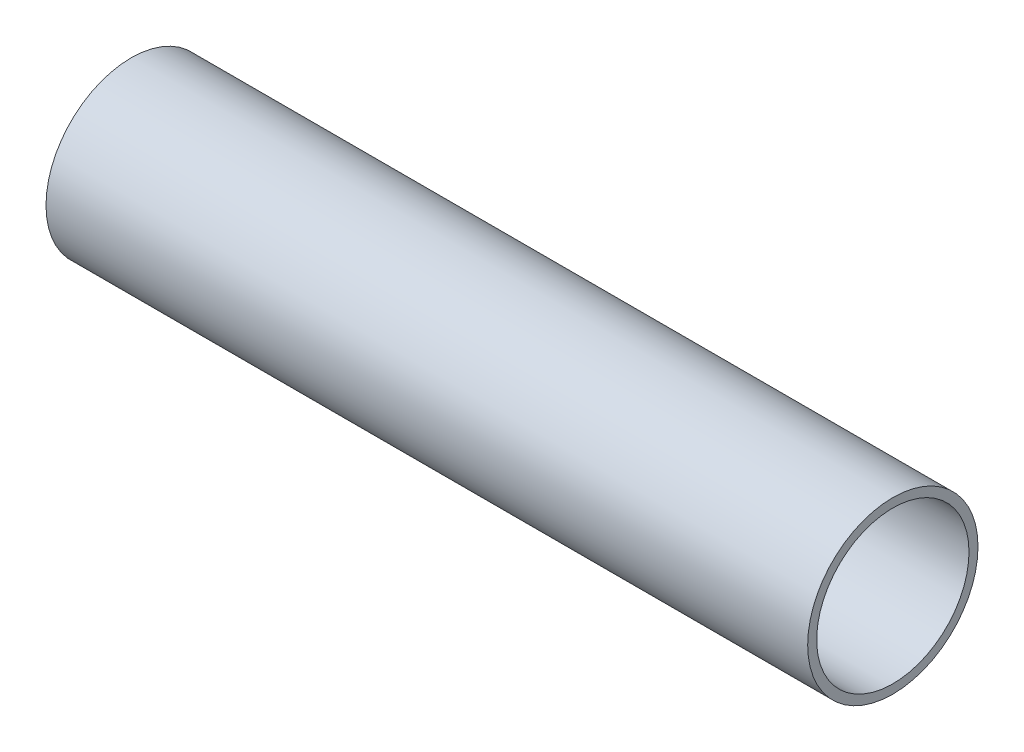
SolidWorks part; units mm, degrees
ref_plane "Front Plane" through (0, 0, 0) normal (0, 0, 1) x (1, 0, 0)
ref_plane "Top Plane" through (0, 0, 0) normal (0, 1, 0) x (1, 0, 0)
ref_plane "Right Plane" through (0, 0, 0) normal (1, 0, 0) x (0, 0, -1)
sketch "Sketch1" plane through (0, 0, 0) normal (1, 0, 0) x (0, 0, -1)
  circle A0 centre (0, 0) radius 50.8
  circle A1 centre (0, 0) radius 56.8
  dimension "D1" = 101.6
  dimension "D2" = 6
extrude "Boss-Extrude1" add sketch "Sketch1" along normal blind 508
